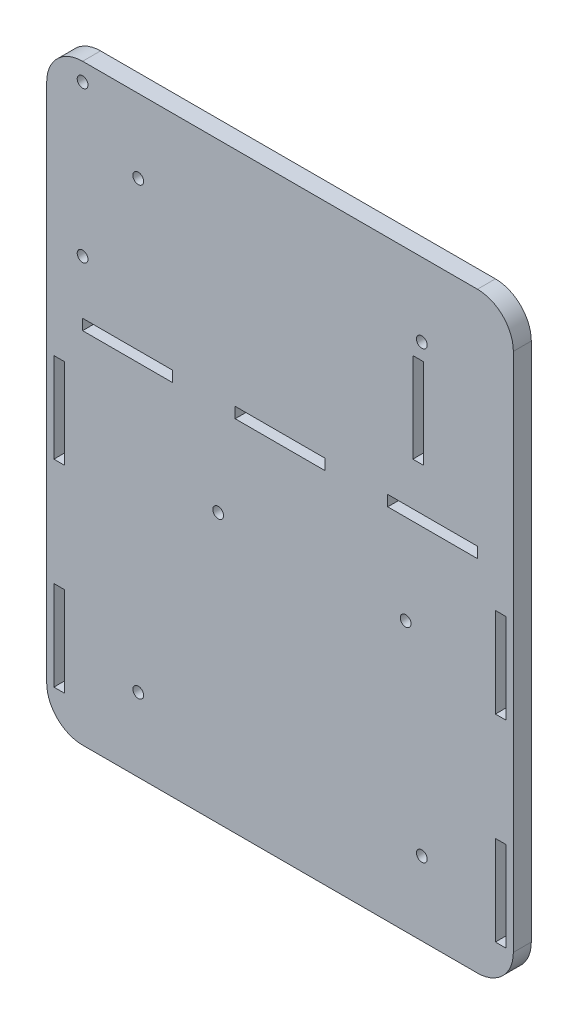
SolidWorks part; units mm, degrees
material "Acrílico (médio-alto impacto)"
ref_plane "Plano frontal" through (0, 0, 0) normal (0, 0, 1) x (1, 0, 0)
ref_plane "Plano superior" through (0, 0, 0) normal (0, 1, 0) x (1, 0, 0)
ref_plane "Plano direito" through (0, 0, 0) normal (1, 0, 0) x (0, 0, -1)
sketch "Esboço1" plane through (0, 0, 0) normal (0, 0, 1) x (1, 0, 0)
  line L1 (-49.2171, -36.3939) -> (60.7829, -36.3939)
  line L2 (-59.2171, -26.3939) -> (-59.2171, 118.6061)
  line L3 (-49.2171, 128.6061) -> (60.7829, 128.6061)
  line L4 (70.7829, -26.3939) -> (70.7829, 118.6061)
  arc A0 (-59.2171, 118.6061) -> (-49.2171, 128.6061) centre (-49.2171, 118.6061) cw
  arc A1 (60.7829, 128.6061) -> (70.7829, 118.6061) centre (60.7829, 118.6061) cw
  arc A2 (60.7829, -36.3939) -> (70.7829, -26.3939) centre (60.7829, -26.3939) ccw
  arc A3 (-49.2171, -36.3939) -> (-59.2171, -26.3939) centre (-49.2171, -26.3939) cw
  dimension "D1" = 10
extrude "Ressalto-extrusão1" add sketch "Esboço1" along normal blind 5
sketch "Esboço2" plane through (0, 0, 0) normal (0, 0, -1) x (-1, 0, 0)
  line L1 (-70.7829, -26.3939) -> (-70.7829, 118.6061) construction
  line L2 (59.2171, 118.6061) -> (59.2171, -26.3939) construction
  line L4 (-60.7829, 128.6061) -> (49.2171, 128.6061) construction
  circle A0 centre (33.7171, -15.8939) radius 1.5
  circle A1 centre (33.7171, 108.1061) radius 1.5
  circle A2 centre (-45.2829, -15.8939) radius 1.5
  circle A3 centre (-45.2829, 108.1061) radius 1.5
  dimension "D1" = 79
  dimension "D2" = 124
  dimension "D3" = 124
  dimension "D4" = 79
  dimension "D5" = 3
  dimension "D6" = 3
  dimension "D7" = 3
  dimension "D8" = 3
  dimension "D9" = 25.5
  dimension "D10" = 25.5
  dimension "D11" = 25.5
  dimension "D12" = 25.5
  dimension "D13" = 20.5
extrude "Corte-extrusão1" cut sketch "Esboço2" against normal blind 5
sketch "Esboço3" plane through (0, 0, 0) normal (0, 0, -1) x (-1, 0, 0)
  line L0 (-60.7829, 128.6061) -> (49.2171, 128.6061) construction
  line L1 (59.2171, 118.6061) -> (59.2171, -26.3939) construction
  circle A0 centre (49.2171, 123.6061) radius 1.5
  circle A1 centre (49.2171, 81.5561) radius 1.5
  dimension "D1" = 5
  dimension "D2" = 3
  dimension "D3" = 3
  dimension "D4" = 42.05
  dimension "D5" = 10
  dimension "D6" = 10
extrude "Corte-extrusão2" cut sketch "Esboço3" against normal through all
sketch "Esboço6" plane through (0, 0, 0) normal (0, 0, -1) x (-1, 0, 0)
  line L0 (49.2171, -36.3939) -> (-60.7829, -36.3939) construction
  line L1 (-68.7829, -26.3939) -> (-65.7829, -26.3939)
  line L2 (-68.7829, -26.3939) -> (-68.7829, -1.3939)
  line L3 (-68.7829, -1.3939) -> (-65.7829, -1.3939)
  line L4 (-65.7829, -26.3939) -> (-65.7829, -1.3939)
  line L5 (-68.7829, 28.6061) -> (-65.7829, 28.6061)
  line L6 (-68.7829, 28.6061) -> (-68.7829, 53.6061)
  line L7 (-68.7829, 53.6061) -> (-65.7829, 53.6061)
  line L8 (-65.7829, 28.6061) -> (-65.7829, 53.6061)
  line L9 (-60.7829, 63.6061) -> (-35.7829, 63.6061)
  line L10 (-60.7829, 63.6061) -> (-60.7829, 66.6061)
  line L11 (-60.7829, 66.6061) -> (-35.7829, 66.6061)
  line L12 (-35.7829, 63.6061) -> (-35.7829, 66.6061)
  line L13 (24.2171, 63.6061) -> (49.2171, 63.6061)
  line L14 (24.2171, 63.6061) -> (24.2171, 66.6061)
  line L15 (24.2171, 66.6061) -> (49.2171, 66.6061)
  line L16 (49.2171, 63.6061) -> (49.2171, 66.6061)
  line L17 (57.2171, 53.6061) -> (54.2171, 53.6061)
  line L18 (57.2171, 53.6061) -> (57.2171, 28.6061)
  line L19 (57.2171, 28.6061) -> (54.2171, 28.6061)
  line L20 (54.2171, 53.6061) -> (54.2171, 28.6061)
  line L21 (57.2171, -1.3939) -> (54.2171, -1.3939)
  line L22 (57.2171, -1.3939) -> (57.2171, -26.3939)
  line L23 (57.2171, -26.3939) -> (54.2171, -26.3939)
  line L24 (54.2171, -1.3939) -> (54.2171, -26.3939)
  line L25 (-70.7829, -26.3939) -> (-70.7829, 118.6061) construction
  line L26 (59.2171, 118.6061) -> (59.2171, -26.3939) construction
  line L28 (-18.2829, 63.6061) -> (6.7171, 63.6061)
  line L29 (-18.2829, 63.6061) -> (-18.2829, 66.6061)
  line L30 (-18.2829, 66.6061) -> (6.7171, 66.6061)
  line L31 (6.7171, 63.6061) -> (6.7171, 66.6061)
  point P26 (-70.7829, 46.1061)
  dimension "D1" = 10
  dimension "D2" = 30
  dimension "D3" = 25
  dimension "D4" = 25
  dimension "D5" = 2
  dimension "D6" = 3
  dimension "D7" = 3
  dimension "D8" = 2
  dimension "D9" = 10
  dimension "D10" = 25
  dimension "D11" = 3
  dimension "D12" = 10
  dimension "D13" = 3
  dimension "D14" = 25
  dimension "D15" = 25
  dimension "D16" = 3
  dimension "D17" = 17.5
  dimension "D18" = 10
  dimension "D19" = 25
  dimension "D20" = 3
  dimension "D21" = 3
  dimension "D22" = 25
  dimension "D23" = 2
  dimension "D24" = 2
  dimension "D25" = 100
  dimension "D26" = 100
  dimension "D27" = 100
  dimension "D28" = 30
extrude "Corte-extrusão4" cut sketch "Esboço6" against normal through all
sketch "Esboço8" plane through (0, 0, 5) normal (0, 0, 1) x (1, 0, 0)
  line L0 (-49.2171, -36.3939) -> (60.7829, -36.3939) construction
  line L1 (-59.2171, 118.6061) -> (-59.2171, -26.3939) construction
  line L2 (70.7829, -26.3939) -> (70.7829, 118.6061) construction
  circle A0 centre (-11.4471, 38.6061) radius 1.5
  circle A1 centre (40.7829, 38.6061) radius 1.5
  dimension "D1" = 3
  dimension "D2" = 75
  dimension "D3" = 47.77
  dimension "D4" = 75
  dimension "D5" = 3
  dimension "D6" = 30
extrude "Corte-extrusão6" cut sketch "Esboço8" against normal blind 10
sketch "Esboço9" plane through (0, 0, 0) normal (0, 0, -1) x (-1, 0, 0)
  line L0 (-60.7829, 128.6061) -> (49.2171, 128.6061) construction
  line L1 (-45.7829, 103.6061) -> (-42.7829, 103.6061)
  line L2 (-45.7829, 103.6061) -> (-45.7829, 78.6061)
  line L3 (-45.7829, 78.6061) -> (-42.7829, 78.6061)
  line L4 (-42.7829, 103.6061) -> (-42.7829, 78.6061)
  line L5 (-70.7829, -26.3939) -> (-70.7829, 118.6061) construction
  dimension "D1" = 25
  dimension "D2" = 3
  dimension "D3" = 25
  dimension "D4" = 25
extrude "Corte-extrusão7" cut sketch "Esboço9" against normal blind 10
